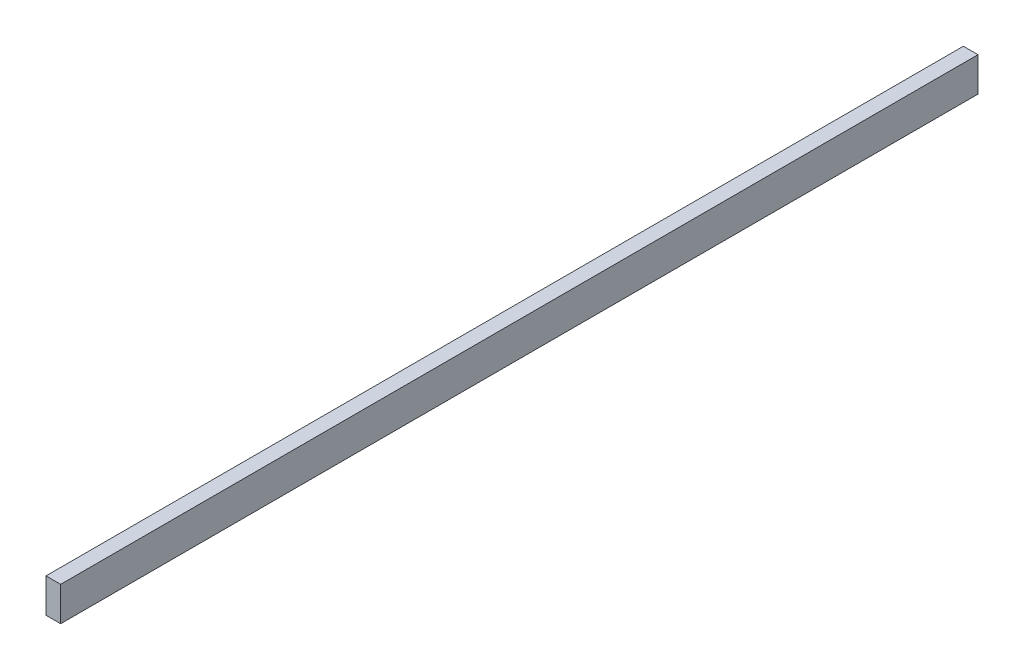
SolidWorks part; units mm, degrees
ref_plane "Front Plane" through (0, 0, 0) normal (0, 0, 1) x (1, 0, 0)
ref_plane "Top Plane" through (0, 0, 0) normal (0, 1, 0) x (1, 0, 0)
ref_plane "Right Plane" through (0, 0, 0) normal (1, 0, 0) x (0, 0, -1)
sketch "Sketch1" plane through (0, 0, 0) normal (1, 0, 0) x (0, 0, -1)
  line L1 (-1193.8, 44.45) -> (1193.8, 44.45)
  line L2 (-1193.8, 44.45) -> (-1193.8, -44.45)
  line L3 (-1193.8, -44.45) -> (1193.8, -44.45)
  line L4 (1193.8, 44.45) -> (1193.8, -44.45)
  line L5 (-1193.8, 44.45) -> (1193.8, -44.45) construction
  line L6 (-1193.8, -44.45) -> (1193.8, 44.45) construction
  point P0 (0, 0)
  dimension "D1" = 88.9
  dimension "D2" = 2387.6
extrude "Boss-Extrude1" add sketch "Sketch1" along normal blind 38.1
